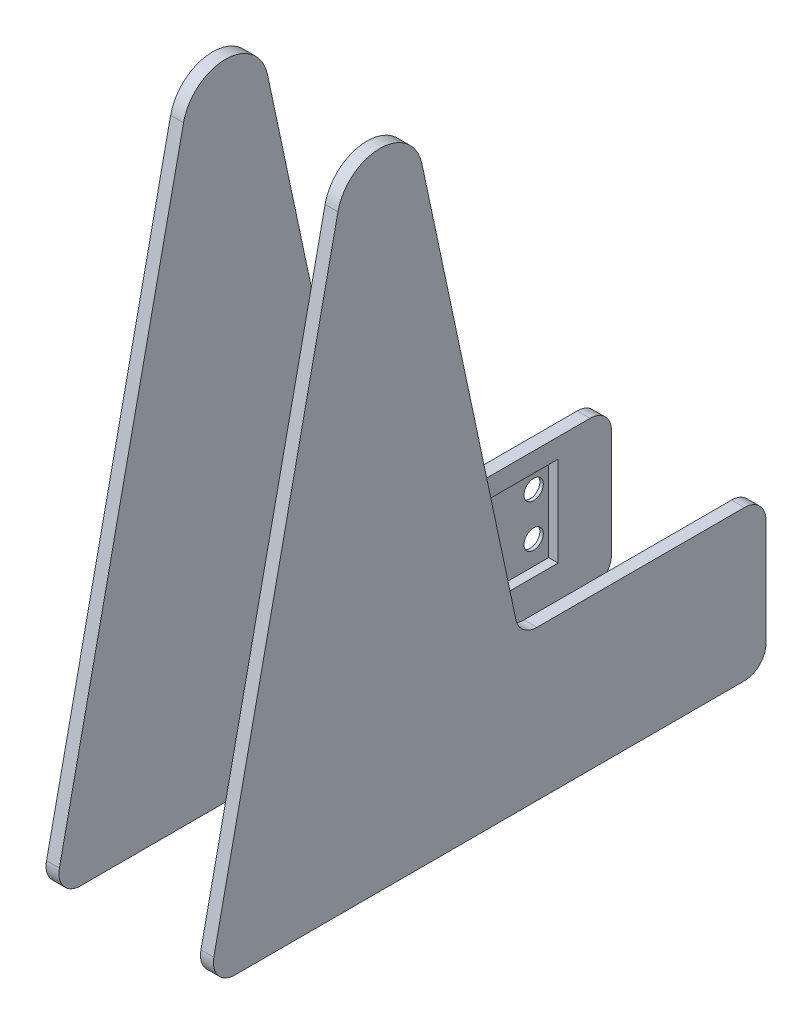
SolidWorks part; units mm, degrees
ref_plane "Front Plane" through (0, 0, 0) normal (0, 0, 1) x (1, 0, 0)
ref_plane "Top Plane" through (0, 0, 0) normal (0, 1, 0) x (1, 0, 0)
ref_plane "Right Plane" through (0, 0, 0) normal (1, 0, 0) x (0, 0, -1)
sketch "nodal" plane through (0, 0, 0) normal (1, 0, 0) x (0, 0, -1)
  line L0 (0, 0) -> (60, 0) construction
  line L1 (0, 0) -> (0, 140) construction
  line L2 (0, 0) -> (60, 0)
  line L3 (0, 0) -> (0, 140)
  line L4 (60, 0) -> (60, 20) construction
  line L5 (60, 0) -> (60, 20)
sketch "motor mount holes" plane through (0, 0, 0) normal (1, 0, 0) x (0, 0, -1)
  arc A40 (74.05, 17) -> (74.05, 13) centre (74.05, 15) ccw construction
  arc A41 (25.55, 13) -> (25.55, 17) centre (25.55, 15) ccw construction
  arc A42 (74.05, 27) -> (74.05, 23) centre (74.05, 25) ccw construction
  arc A43 (25.55, 23) -> (25.55, 27) centre (25.55, 25) ccw construction
  arc A44 (74.05, 17) -> (74.05, 13) centre (74.05, 15) ccw construction
  arc A45 (25.55, 13) -> (25.55, 17) centre (25.55, 15) ccw construction
  arc A46 (74.05, 27) -> (74.05, 23) centre (74.05, 25) ccw construction
  arc A47 (25.55, 23) -> (25.55, 27) centre (25.55, 25) ccw construction
  circle A48 centre (25.55, 25) radius 2
  circle A49 centre (74.05, 25) radius 2
  circle A50 centre (74.05, 15) radius 2
  circle A51 centre (25.55, 15) radius 2
  point P0 (74.05, 15)
  point P3 (25.55, 15)
  point P6 (74.05, 25)
  point P9 (25.55, 25)
ref_plane "Plane1" through (16.5, 0, 0) normal (1, 0, 0) x (0, 0, -1)
ref_plane "Plane2" through (-16.5, 0, 0) normal (1, 0, 0) x (0, 0, -1)
sketch "Sketch3" plane through (16.5, 0, 0) normal (1, 0, 0) x (0, 0, -1)
  line L1 (0, 0) -> (0, 250) construction
  line L2 (-33.8247, 0) -> (0, 0)
  line L3 (0, 0) -> (0, 150) construction
  line L5 (-9.7812, 142.0803) -> (-38.7153, 6.0402)
  line L6 (9.7812, 142.0803) -> (38.7153, 6.0402) construction
  line L7 (36.6043, 35) -> (85, 35)
  line L8 (90, 30) -> (90, 5)
  line L9 (85, 0) -> (0, 0)
  line L10 (9.7812, 142.0803) -> (31.7137, 38.9598)
  circle A0 centre (0, 140) radius 10 construction
  arc A1 (-38.7153, 6.0402) -> (-33.8247, 0) centre (-33.8247, 5) ccw
  arc A2 (36.6043, 35) -> (31.7137, 38.9598) centre (36.6043, 40) cw
  arc A3 (85, 0) -> (90, 5) centre (85, 5) ccw
  arc A4 (90, 30) -> (85, 35) centre (85, 30) ccw
  arc A5 (-9.7812, 142.0803) -> (9.7812, 142.0803) centre (0, 140) cw
  point P13 (-40, 0)
  point P20 (32.5559, 35)
  point P23 (90, 0)
  point P26 (90, 35)
  dimension "D1" = 20
  dimension "D3" = 5
  dimension "D6" = 5
  dimension "D7" = 5
  dimension "D2" = 40
  dimension "D4" = 90
  dimension "D5" = 35
extrude "Boss-Extrude1" add sketch "Sketch3" along normal blind 3 contours A5 L5 A1 L2 L9 A3 L8 A4 L7 A2 L10
sketch "motor size" plane through (-16.5, 0, 0) normal (-1, 0, 0) x (0, 0, 1)
  line L0 (-75.05, 30) -> (-69.5, 30) construction
  line L1 (-29.6134, 30) -> (-69.9866, 30) construction
  line L2 (-29.6134, 30) -> (-29.6134, 10) construction
  line L3 (-29.6134, 10) -> (-69.9866, 10) construction
  line L4 (-69.9866, 30) -> (-69.9866, 10) construction
  line L5 (-69.5, 10) -> (-75.05, 10) construction
  line L6 (-29.6134, 10.5) -> (-29.6134, 29.5) construction
  line L7 (-69.9866, 29.5) -> (-69.9866, 10.5) construction
  line L8 (-69.9866, 30) -> (-29.6134, 10) construction
  line L9 (-29.6134, 30) -> (-69.9866, 10) construction
  point P4 (-49.8, 20)
sketch "Sketch5" plane through (-16.5, 0, 0) normal (-1, 0, 0) x (0, 0, 1)
  line L0 (-69.9866, 30) -> (-29.6134, 10) construction
  line L1 (-70.3866, 30.4) -> (-29.2134, 30.4)
  line L2 (-70.3866, 30.4) -> (-70.3866, 9.6)
  line L3 (-70.3866, 9.6) -> (-29.2134, 9.6)
  line L4 (-29.2134, 30.4) -> (-29.2134, 9.6)
  line L5 (-70.3866, 30.4) -> (-29.2134, 9.6) construction
  line L6 (-70.3866, 9.6) -> (-29.2134, 30.4) construction
  line L7 (-29.6134, 30) -> (-69.9866, 30) construction
  line L8 (-29.6134, 30) -> (-29.6134, 10) construction
  point P0 (-49.8, 20)
  dimension "D1" = 0.4
  dimension "D2" = 0.4
mirror "Mirror2" about plane through (0, 0, 0) normal (1, 0, 0) of bodies 101
ref_plane "Plane3" through (-18.7, 0, 0) normal (-1, 0, 0) x (0, 0, 1)
sketch "Sketch6" plane through (-18.7, 0, 0) normal (-1, 0, 0) x (0, 0, 1)
  line L0 (-22.55, 28) -> (-22.55, 26.25) construction
  line L1 (-77.05, 29.9866) -> (-22.55, 29.9866) construction
  line L2 (-77.05, 29.9866) -> (-77.05, 10) construction
  line L3 (-77.05, 10) -> (-22.55, 10) construction
  line L4 (-22.55, 29.9866) -> (-22.55, 10) construction
  line L5 (-77.05, 29.9866) -> (-22.55, 10) construction
  line L6 (-77.05, 10) -> (-22.55, 29.9866) construction
  line L7 (-30.1, 29.9866) -> (-69.5, 29.9866) construction
  line L8 (-77.05, 26.25) -> (-77.05, 28) construction
  line L9 (-30.1, 10) -> (-69.5, 10) construction
  line L11 (-77.55, 30.4866) -> (-22.05, 30.4866)
  line L12 (-77.55, 30.4866) -> (-77.55, 9.5)
  line L13 (-77.55, 9.5) -> (-22.05, 9.5)
  line L14 (-22.05, 30.4866) -> (-22.05, 9.5)
  line L15 (-77.55, 30.4866) -> (-22.05, 9.5) construction
  line L16 (-77.55, 9.5) -> (-22.05, 30.4866) construction
  point P0 (-49.8, 19.9933)
  point P13 (-49.8, 19.9933)
  dimension "D1" = 0.5
  dimension "D2" = 0.5
extrude "Cut-Extrude1" cut sketch "Sketch6" against normal up to next (2.2 mm away)
sketch "Sketch11" plane through (-18.7, 0, 0) normal (-1, 0, 0) x (0, 0, 1)
  circle A1 centre (-25.55, 15) radius 2
  circle A2 centre (-25.55, 15) radius 2
  circle A3 centre (-74.05, 15) radius 2
  circle A4 centre (-74.05, 15) radius 2
  circle A5 centre (-74.05, 25) radius 2
  circle A6 centre (-74.05, 25) radius 2
  circle A7 centre (-25.55, 25) radius 2
  circle A8 centre (-25.55, 25) radius 2
  point P2 (-25.55, 15)
  point P5 (-74.05, 15)
  point P8 (-74.05, 25)
  point P11 (-25.55, 25)
  dimension "D1" = 0
  dimension "D2" = 0
  dimension "D3" = 0
  dimension "D4" = 0
hole_wizard "M4 Clearance Hole1" positions "Sketch11" profile "Sketch12" hole size "M4" standard "ANSI Metric" end condition through all
sketch "Sketch12" plane through (-18.7, 15, -25.55) normal (0, 1, 0) x (0, 0, -1)
  line L0 (0, 0) -> (0, 0.8)
  line L1 (0, 0.8) -> (2.25, 0.8)
  line L2 (2.25, 0.8) -> (2.25, 0)
  line L5 (2.25, 0) -> (0, 0)
  line L11 (0, -6.35) -> (0, 107.95) construction
  dimension "Thru Hole Dia." = 4.5
  dimension "Thru Hole Depth" = 0.8
equation "\"motor center z\" = 60mm"
equation "\"motor center y\" = 20mm"
equation "\"link 1\" = 40mm"
equation "\"link 2\"= 90mm"
equation "\"pivot height\"= 140mm"
equation "\"camera height\" = 250mm"
equation "\"link 1 thickness\" = 6mm"
equation "\"link height\" = 20mm"
equation "\"pivot size\" = 6mm"
equation "\"D2@Sketch3\"=\"motor center z\"*2/3"
equation "\"D4@Sketch3\"=\"motor center z\"*3/2"
equation "\"D5@Sketch3\"=\"motor center y\"*7/4"
equation "\"beam length\" = 120mm"
equation "\"beam thickness\"= 50mm"
equation "\"beam width\" = 27mm"
equation "\"beam side wall thickness\" = 3mm"
